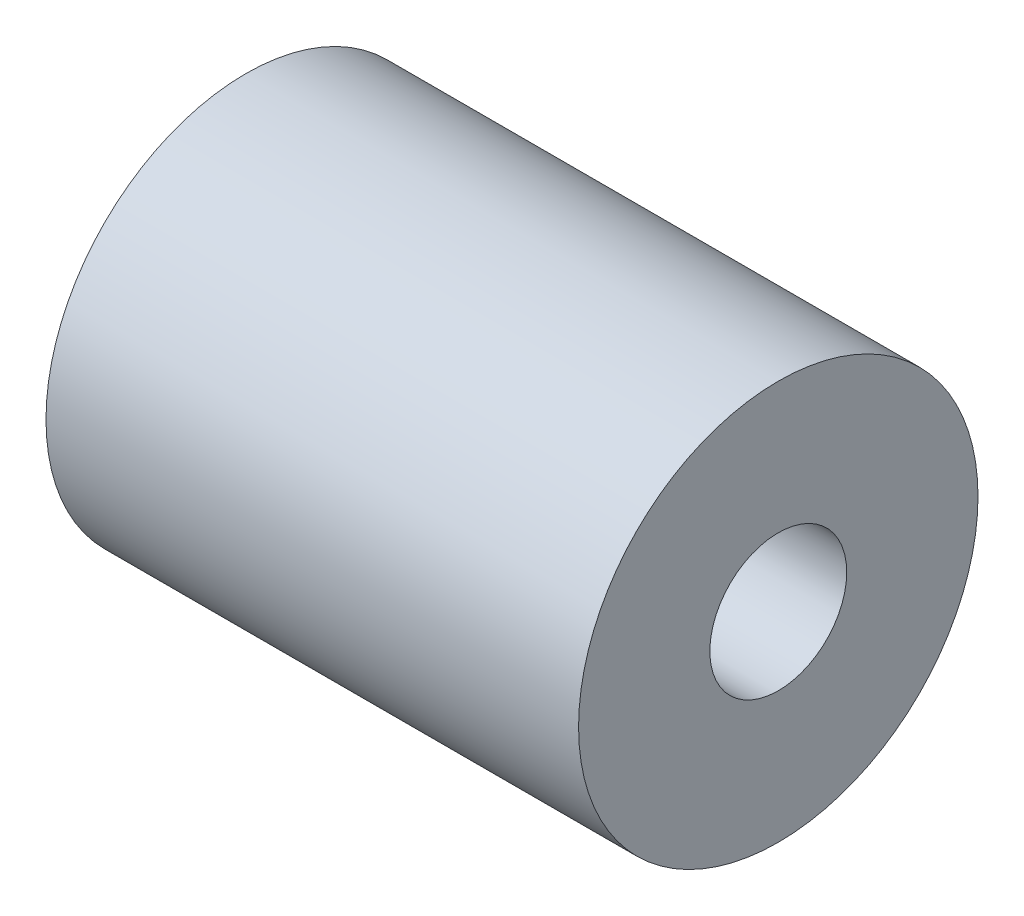
SolidWorks part; units mm, degrees
material "ABS"
ref_plane "Front Plane" through (0, 0, 0) normal (0, 0, 1) x (1, 0, 0)
ref_plane "Top Plane" through (0, 0, 0) normal (0, 1, 0) x (1, 0, 0)
ref_plane "Right Plane" through (0, 0, 0) normal (1, 0, 0) x (0, 0, -1)
sketch "Sketch1" plane through (0, 0, 0) normal (1, 0, 0) x (0, 0, -1)
  circle A0 centre (0, 0) radius 3.2639
  circle A1 centre (0, 0) radius 9.525
  dimension "D1" = 6.5278
  dimension "D2" = 19.05
extrude "Boss-Extrude1" add sketch "Sketch1" along normal blind 25.4
